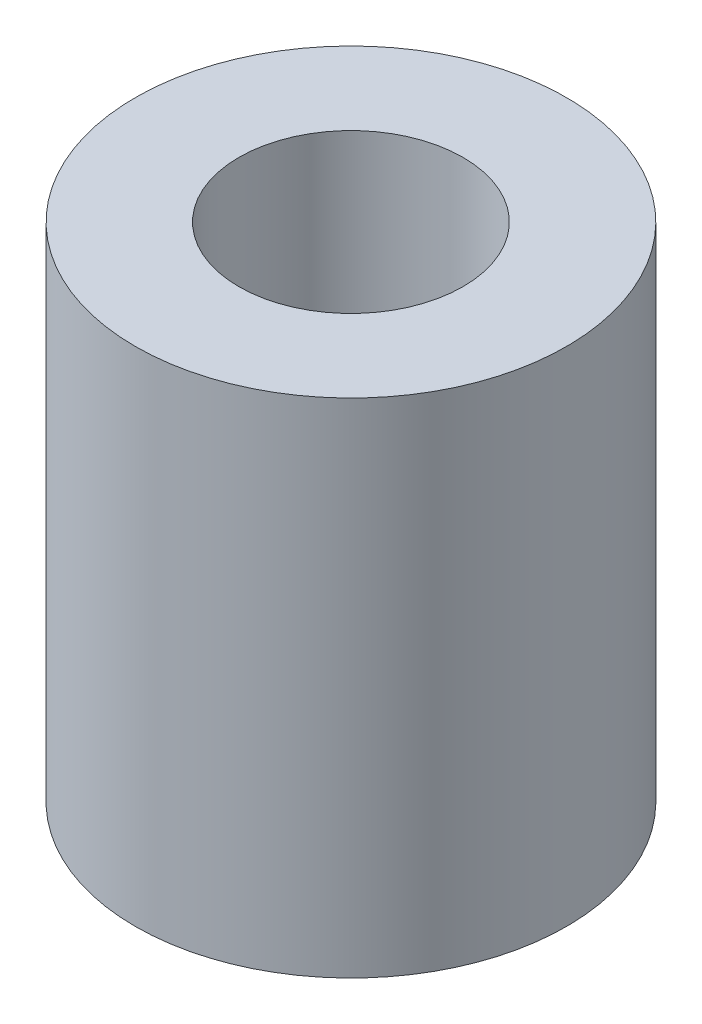
SolidWorks part; units mm, degrees
material "PLA"
ref_plane "Front Plane" through (0, 0, 0) normal (0, 0, 1) x (1, 0, 0)
ref_plane "Top Plane" through (0, 0, 0) normal (0, 1, 0) x (1, 0, 0)
ref_plane "Right Plane" through (0, 0, 0) normal (1, 0, 0) x (0, 0, -1)
sketch "Sketch1" plane through (0, 0, 0) normal (0, 1, 0) x (1, 0, 0)
  circle A0 centre (0, 0) radius 6.35
  circle A1 centre (0, 0) radius 3.3
  dimension "D1" = 12.7
  dimension "D2" = 6.6
extrude "Boss-Extrude1" add sketch "Sketch1" along normal blind 14.7955
